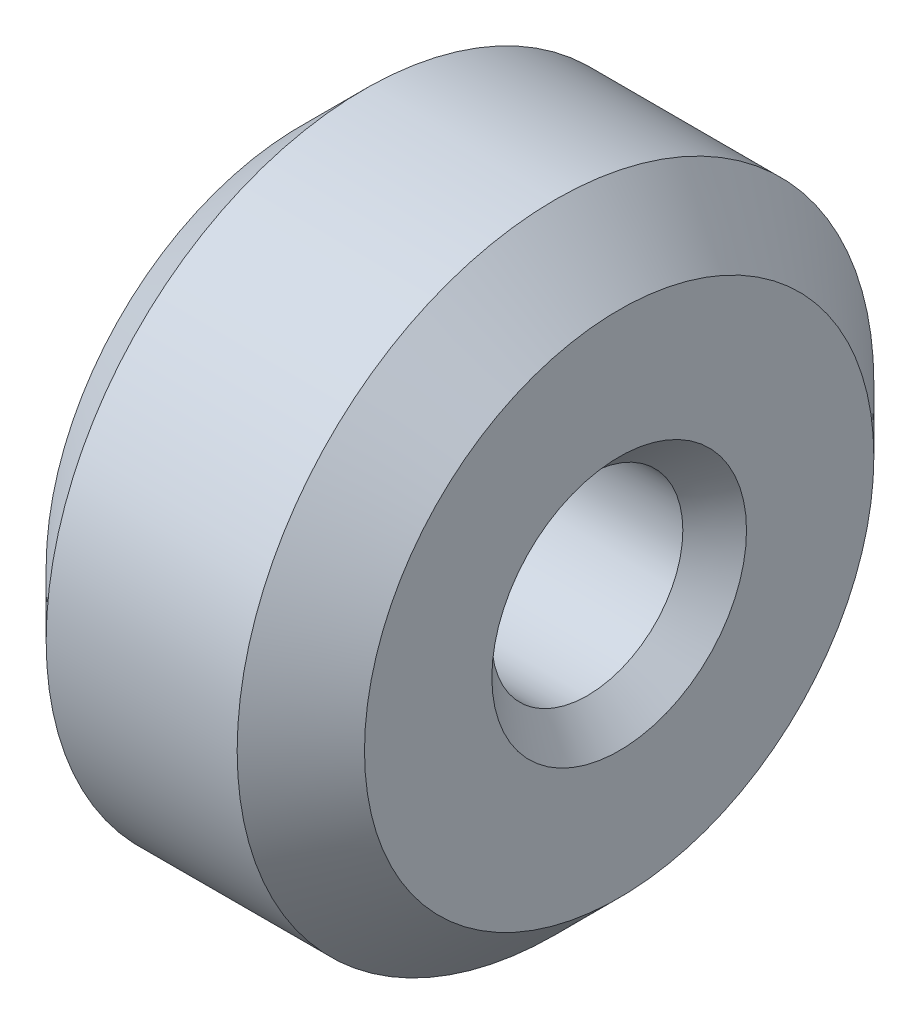
SolidWorks part; units mm, degrees
ref_plane "Front Plane" through (0, 0, 0) normal (0, 0, 1) x (1, 0, 0)
ref_plane "Top Plane" through (0, 0, 0) normal (0, 1, 0) x (1, 0, 0)
ref_plane "Right Plane" through (0, 0, 0) normal (1, 0, 0) x (0, 0, -1)
sketch "Sketch1" plane through (0, 0, 0) normal (0, 0, 1) x (1, 0, 0)
  line L0 (0, 0) -> (50000, 0) construction
  line L1 (0, 0) -> (0, 10)
  line L2 (0, 10) -> (10, 10)
  line L3 (10, 10) -> (10, 0)
  line L4 (0, 3) -> (10, 3)
  dimension "D1" = 10
  dimension "D2" = 20
  dimension "D3" = 6
revolve "Revolve2" add sketch "Sketch1" angle 360 about L0
chamfer "Chamfer1" distance 2 angle 45 2 edges at (0, 0, 10) (10, 0, 10)
chamfer "Chamfer2" distance 1 angle 45 1 edges at (10, 0, 3)
